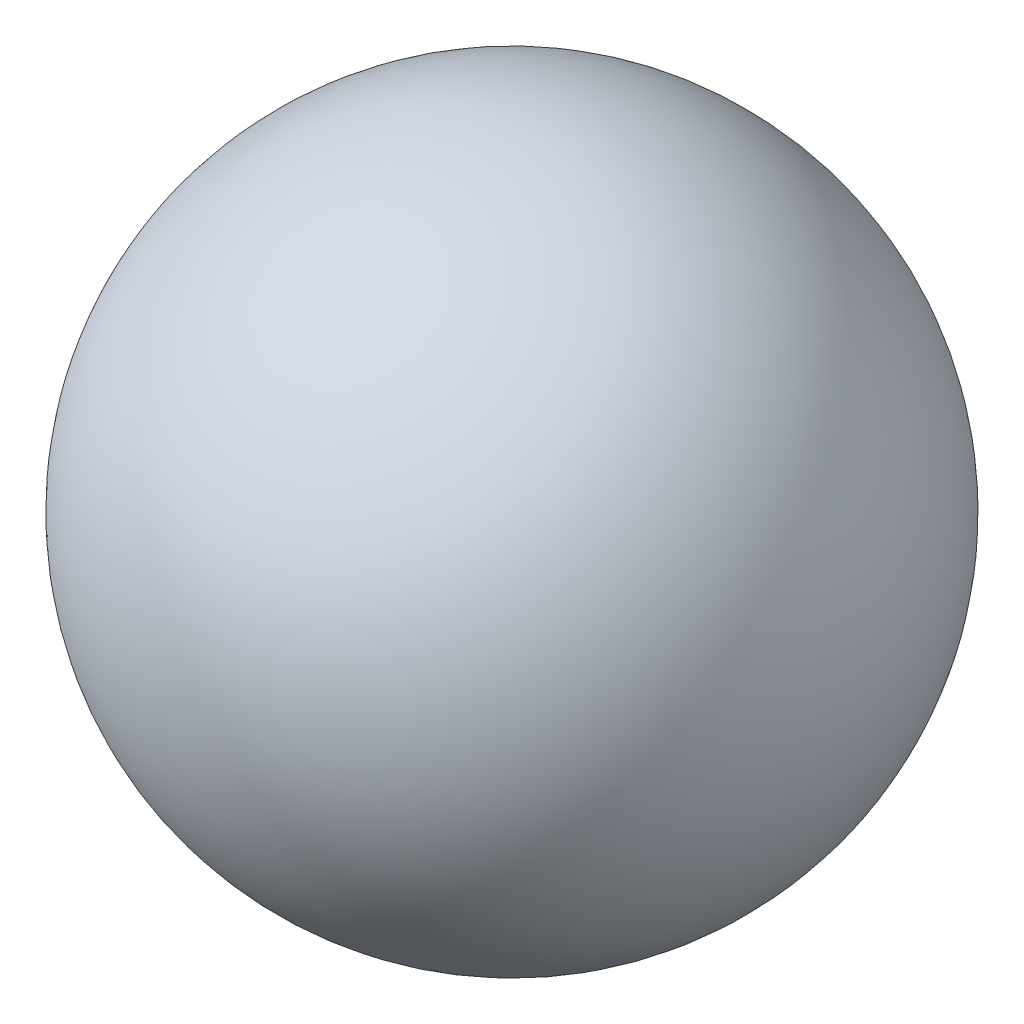
SolidWorks part; units mm, degrees
material "AISI 1020"
ref_plane "Front Plane" through (0, 0, 0) normal (0, 0, 1) x (1, 0, 0)
ref_plane "Top Plane" through (0, 0, 0) normal (0, 1, 0) x (1, 0, 0)
ref_plane "Right Plane" through (0, 0, 0) normal (1, 0, 0) x (0, 0, -1)
sketch "Sketch1" plane through (0, 0, 0) normal (0, 0, 1) x (1, 0, 0)
  line L0 (-1, 0) -> (1, 0)
  arc A0 (1, 0) -> (-1, 0) centre (0, 0) ccw
  dimension "D1" = 2
revolve "Revolve1" add sketch "Sketch1" angle 360 about L0
